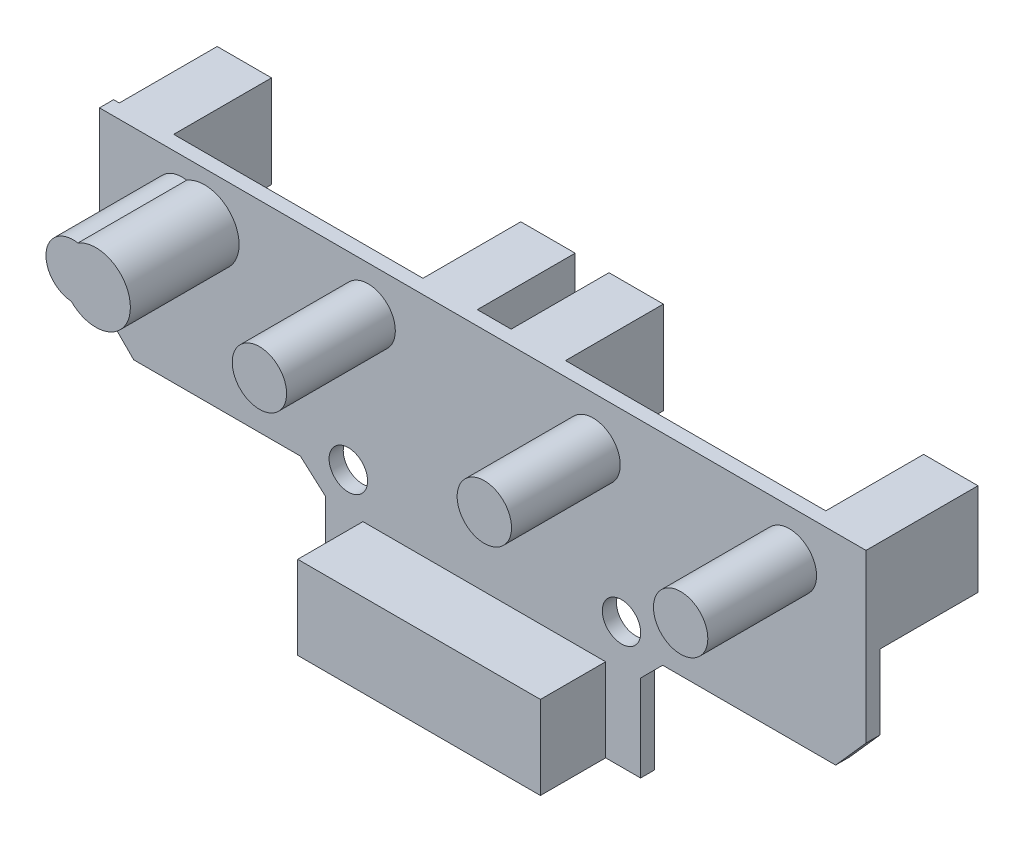
SolidWorks part; units mm, degrees
ref_plane "前视基准面" through (0, 0, 0) normal (0, 0, 1) x (1, 0, 0)
ref_plane "上视基准面" through (0, 0, 0) normal (0, 1, 0) x (1, 0, 0)
ref_plane "右视基准面" through (0, 0, 0) normal (1, 0, 0) x (0, 0, -1)
sketch "草图1" plane through (0, 0, 0) normal (0, 0, 1) x (1, 0, 0)
  line L0 (-70.5, -15.347) -> (-67.347, -18.5)
  line L1 (0, 0) -> (-70.5, 0)
  line L2 (0, 0) -> (0, -15.347)
  line L3 (-2.7926, -18.5) -> (-18.7003, -18.5)
  line L4 (-70.5, 0) -> (-70.5, -15.347)
  line L6 (-49.7316, -20.5313) -> (-49.7316, -28.5)
  line L7 (-49.7316, -28.5) -> (-20.7316, -28.5)
  line L8 (-20.7316, -20.5313) -> (-20.7316, -28.5)
  line L9 (-67.347, -18.5) -> (-52.025, -18.5)
  line L10 (-2.7926, -18.5) -> (0, -15.347)
  line L11 (-52.025, -18.5) -> (-67.347, -18.5)
  line L12 (-52.025, -18.5) -> (-49.7316, -20.5313)
  line L13 (-20.7316, -20.5313) -> (-18.7003, -18.5)
  line L14 (-18.7003, -18.5) -> (-2.7926, -18.5)
  dimension "D1" = 70.5
  dimension "D3" = 29
extrude "凸台-拉伸1" add sketch "草图1" along normal blind 1.3 contours L8 L13 L3 L10 L2 L1 L4 L0 L9 L12 L6 L7
sketch "草图2" plane through (-0.9019, 0, 0) normal (0, 0, -1) x (-1, 0, 0)
  circle A0 centre (38.8224, -18.2631) radius 0.0001
  circle A1 centre (24.0948, -18.2631) radius 1.8547
extrude "切除-拉伸1" cut sketch "草图2" against normal blind 1.3
sketch "草图3" plane through (0, 0, 0) normal (0, 0, -1) x (-1, 0, 0)
  line L0 (0, 0) -> (70.5, 0) construction
  line L1 (0, 0) -> (5, 0)
  line L2 (0, 0) -> (0, -8.5)
  line L3 (0, -8.5) -> (5, -8.5)
  line L4 (5, 0) -> (5, -8.5)
  line L5 (33.9378, 0) -> (28.9378, 0)
  line L6 (33.9378, 0) -> (33.9378, -8.5)
  line L7 (33.9378, -8.5) -> (28.9378, -8.5)
  line L8 (28.9378, 0) -> (28.9378, -8.5)
  line L10 (37.0496, 0) -> (42.0496, 0)
  line L11 (37.0496, 0) -> (37.0496, -8.5)
  line L12 (37.0496, -8.5) -> (42.0496, -8.5)
  line L13 (42.0496, 0) -> (42.0496, -8.5)
  line L14 (69.9755, 0) -> (64.9755, 0)
  line L15 (69.9755, 0) -> (69.9755, -8.5)
  line L16 (69.9755, -8.5) -> (64.9755, -8.5)
  line L17 (64.9755, 0) -> (64.9755, -8.5)
  dimension "D1" = 8.5
  dimension "D2" = 5
  dimension "D3" = 5
  dimension "D4" = 5
  dimension "D5" = 5
extrude "凸台-拉伸2" add sketch "草图3" along normal blind 9
sketch "草图4" plane through (0, 0, 1.3) normal (0, 0, 1) x (1, 0, 0)
  line L0 (-49.7316, -28.5) -> (-20.7316, -28.5) construction
  line L1 (-46.2686, -28.5) -> (-23.9458, -28.5)
  line L2 (-46.2686, -28.5) -> (-46.2686, -20.8434)
  line L3 (-46.2686, -20.8434) -> (-23.9458, -20.8434)
  line L4 (-23.9458, -28.5) -> (-23.9458, -20.8434)
extrude "凸台-拉伸3" add sketch "草图4" along normal blind 6 contours L2 L1 L4 L3
sketch "草图7" plane through (0, 0, 0) normal (0, 0, -1) x (-1, 0, 0)
  circle A1 centre (24.9967, -18.2631) radius 2.0609
  circle A2 centre (22.9227, -19.6884) radius 0.0094
  circle A3 centre (0, 0) radius 1
extrude "凸台-拉伸6" add sketch "草图7" against normal blind 1.3
sketch "草图9" plane through (0, 0, 0) normal (0, 0, -1) x (-1, 0, 0)
  circle A0 centre (22.4861, -16.9324) radius 1.7666
  circle A1 centre (47.6124, -17.3942) radius 1.77
extrude "切除-拉伸4" cut sketch "草图9" against normal blind 13.5
sketch "草图11" plane through (0, 0, 1.3) normal (0, 0, 1) x (1, 0, 0)
  circle A0 centre (-7.0497, -4.2991) radius 2.5
  circle A1 centre (-25.1054, -4.5014) radius 2.5
  circle A2 centre (-45.79, -4.1609) radius 2.5
  circle A3 centre (-62.9236, -4.2171) radius 2.5
extrude "凸台-拉伸7" add sketch "草图11" along normal blind 10
sketch "草图5" plane through (0, 0, 1.3) normal (0, 0, 1) x (1, 0, 0)
  circle A0 centre (-48.2814, -4.1273) radius 3.1887
  circle A1 centre (-60.837, -4.474) radius 3.1779
  circle A2 centre (-24.5218, -4.2094) radius 2.722
  circle A3 centre (-9.1889, -4.3552) radius 3.1853
extrude "凸台-拉伸4" add sketch "草图5" along normal blind 10 contours A1
